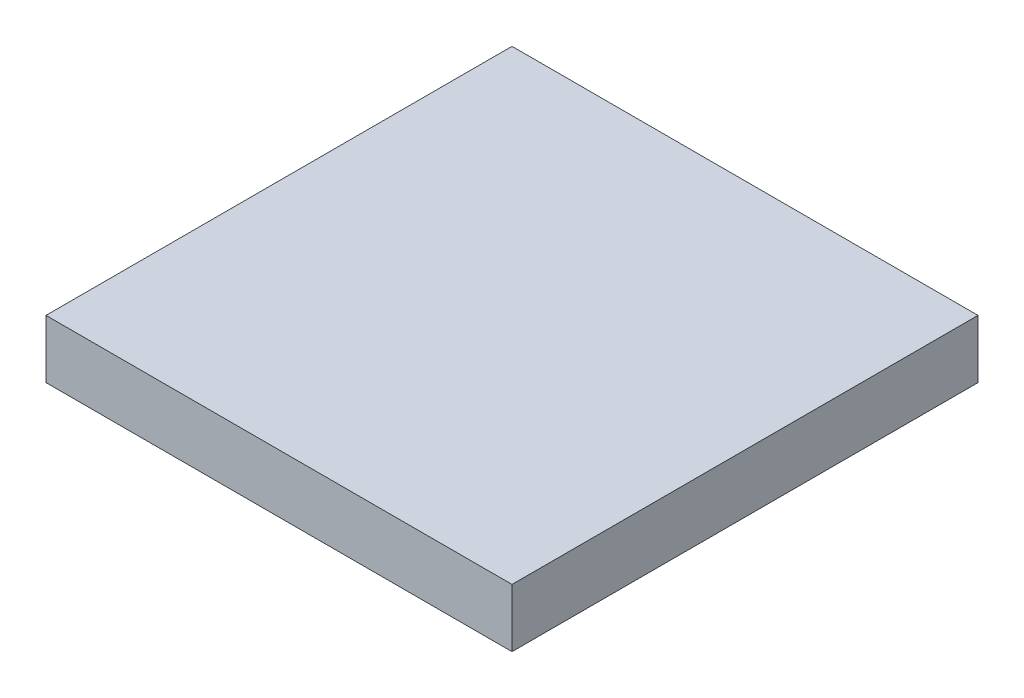
SolidWorks part; units mm, degrees
ref_plane "Front Plane" through (0, 0, 0) normal (0, 0, 1) x (1, 0, 0)
ref_plane "Top Plane" through (0, 0, 0) normal (0, 1, 0) x (1, 0, 0)
ref_plane "Right Plane" through (0, 0, 0) normal (1, 0, 0) x (0, 0, -1)
sketch "Sketch1" plane through (0, 0, 0) normal (0, 1, 0) x (1, 0, 0)
  line L1 (-0.2, 0.2) -> (0.2, 0.2)
  line L2 (-0.2, 0.2) -> (-0.2, -0.2)
  line L3 (-0.2, -0.2) -> (0.2, -0.2)
  line L4 (0.2, 0.2) -> (0.2, -0.2)
extrude "Boss-Extrude1" add sketch "Sketch1" along normal blind 0.05
